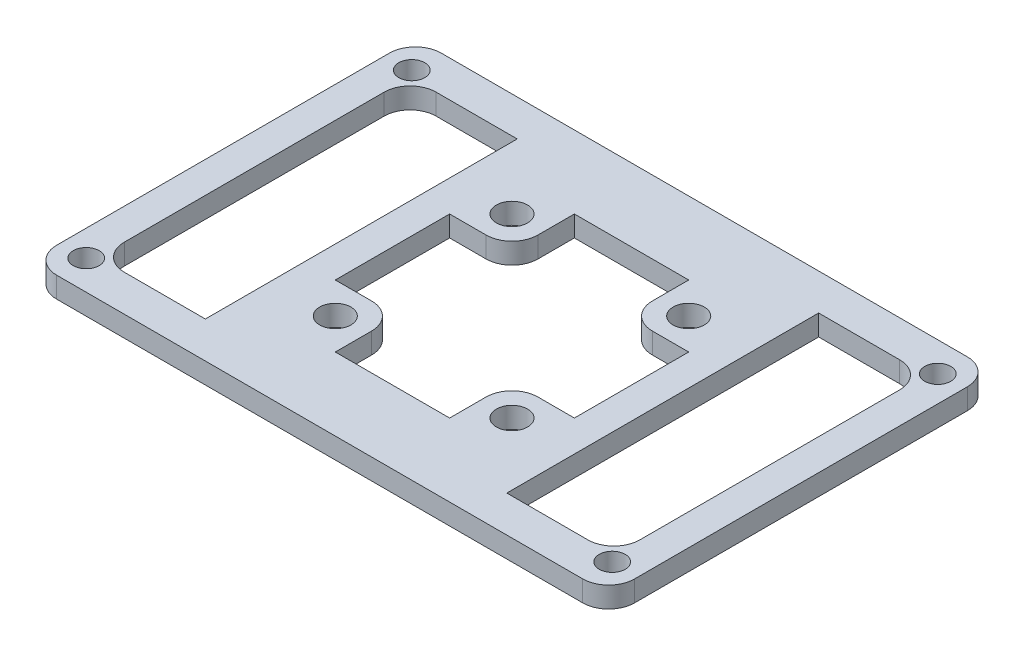
SolidWorks part; units mm, degrees
ref_plane "Front Plane" through (0, 0, 0) normal (0, 0, 1) x (1, 0, 0)
ref_plane "Top Plane" through (0, 0, 0) normal (0, 1, 0) x (1, 0, 0)
ref_plane "Right Plane" through (0, 0, 0) normal (1, 0, 0) x (0, 0, -1)
sketch "Sketch1" plane through (0, 0, 0) normal (0, 1, 0) x (1, 0, 0)
  line L1 (-27.8, 18.5) -> (27.8, 18.5)
  line L2 (-27.8, 18.5) -> (-27.8, -18.5)
  line L3 (-27.8, -18.5) -> (27.8, -18.5)
  line L4 (27.8, 18.5) -> (27.8, -18.5)
  line L5 (-27.8, 18.5) -> (27.8, -18.5) construction
  line L6 (-27.8, -18.5) -> (27.8, 18.5) construction
  point P0 (0, 0)
  dimension "D1" = 37
  dimension "D2" = 55.6
extrude "Boss-Extrude1" add sketch "Sketch1" along normal blind 2
sketch "Sketch3" plane through (0, 2, 0) normal (0, 1, 0) x (1, 0, 0)
  line L0 (0, 8.5) -> (0, -8.5) construction
  line L1 (-8.5, 8.5) -> (8.5, 8.5)
  line L2 (-8.5, 8.5) -> (-8.5, -8.5)
  line L3 (-8.5, -8.5) -> (8.5, -8.5)
  line L4 (8.5, 8.5) -> (8.5, -8.5)
  line L5 (-8.5, 8.5) -> (8.5, -8.5) construction
  line L6 (-8.5, -8.5) -> (8.5, 8.5) construction
  line L7 (-8.5, 0) -> (8.5, 0) construction
  circle A0 centre (-8.5, 8.5) radius 1.5
  circle A1 centre (-8.5, 8.5) radius 2.5
  circle A2 centre (-8.5, -8.5) radius 2.5
  circle A3 centre (-8.5, -8.5) radius 1.5
  circle A4 centre (8.5, -8.5) radius 1.5
  circle A5 centre (8.5, -8.5) radius 2.5
  circle A6 centre (8.5, 8.5) radius 2.5
  circle A7 centre (8.5, 8.5) radius 1.5
  point P0 (0, 0)
  dimension "D3" = 3
  dimension "D4" = 5
  dimension "D1" = 17
  dimension "D2" = 17
sketch "Sketch5" plane through (0, 2, 0) normal (0, 1, 0) x (1, 0, 0)
  line L0 (0, 11.5) -> (0, -11.5) construction
  line L5 (-11.5, 11.5) -> (11.5, 11.5)
  line L6 (-11.5, 11.5) -> (-11.5, -11.5)
  line L15 (-11.5, -11.5) -> (11.5, -11.5)
  line L16 (11.5, 11.5) -> (11.5, -11.5)
  line L21 (-11.5, 11.5) -> (11.5, -11.5) construction
  line L22 (-11.5, -11.5) -> (11.5, 11.5) construction
  line L23 (-11.5, 11.5) -> (-5.5, 11.5)
  line L24 (-11.5, 11.5) -> (-11.5, 5.5)
  line L25 (-11.5, 5.5) -> (-8, 5.5)
  line L26 (-5.5, 11.5) -> (-5.5, 8)
  line L27 (-11.5, 0) -> (11.5, 0) construction
  line L28 (11.5, 5.5) -> (8, 5.5)
  line L29 (5.5, 11.5) -> (5.5, 8)
  line L30 (11.5, 11.5) -> (5.5, 11.5)
  line L31 (11.5, 11.5) -> (11.5, 5.5)
  line L32 (11.5, -11.5) -> (5.5, -11.5)
  line L33 (5.5, -11.5) -> (5.5, -8)
  line L34 (11.5, -5.5) -> (8, -5.5)
  line L35 (11.5, -11.5) -> (11.5, -5.5)
  line L36 (-11.5, -5.5) -> (-8, -5.5)
  line L37 (-5.5, -11.5) -> (-5.5, -8)
  line L38 (-11.5, -11.5) -> (-5.5, -11.5)
  line L39 (-11.5, -11.5) -> (-11.5, -5.5)
  arc A0 (5.5, -8) -> (8, -5.5) centre (8, -8) cw
  arc A1 (-8, -5.5) -> (-5.5, -8) centre (-8, -8) cw
  arc A2 (8, 5.5) -> (5.5, 8) centre (8, 8) cw
  arc A3 (-8, 5.5) -> (-5.5, 8) centre (-8, 8) ccw
  point P0 (0, 0)
  point P25 (5.5, -5.5)
  point P28 (-5.5, -5.5)
  point P31 (5.5, 5.5)
  point P34 (-5.5, 5.5)
  dimension "D4" = 2.5
  dimension "D1" = 23
  dimension "D2" = 23
  dimension "D3" = 6
extrude "Cut-Extrude2" cut sketch "Sketch5" against normal up to next
fillet "Fillet2" radius 2.5 4 edges at (27.8, 1, -18.5) (-27.8, 1, -18.5) (27.8, 1, 18.5) (-27.8, 1, 18.5)
sketch "Sketch6" plane through (0, 2, 0) normal (0, 1, 0) x (1, 0, 0)
  line L0 (-27.8, 0) -> (-11.5, 0) construction
  line L1 (-27.8, 16) -> (-27.8, -16) construction
  line L2 (-11.5, 5.5) -> (-11.5, -5.5) construction
  line L3 (25.3, 18.5) -> (-25.3, 18.5) construction
  line L4 (-22.3, 15) -> (-14.5, 15)
  line L5 (-24.8, 12.5) -> (-24.8, -12.5)
  line L6 (-22.3, -15) -> (-14.5, -15)
  line L7 (-14.5, 15) -> (-14.5, -15)
  line L8 (-24.8, 15) -> (-14.5, -15) construction
  line L9 (-24.8, -15) -> (-14.5, 15) construction
  line L10 (0, 18.5) -> (0, -18.5) construction
  line L11 (-25.3, -18.5) -> (25.3, -18.5) construction
  line L12 (22.3, -15) -> (14.5, -15)
  line L13 (14.5, 15) -> (14.5, -15)
  line L14 (22.3, 15) -> (14.5, 15)
  line L15 (24.8, 12.5) -> (24.8, -12.5)
  arc A0 (-24.8, -12.5) -> (-22.3, -15) centre (-22.3, -12.5) ccw
  arc A1 (-22.3, 15) -> (-24.8, 12.5) centre (-22.3, 12.5) ccw
  arc A2 (24.8, -12.5) -> (22.3, -15) centre (22.3, -12.5) cw
  arc A3 (22.3, 15) -> (24.8, 12.5) centre (22.3, 12.5) cw
  point P6 (-19.65, 0)
  point P11 (-18.4, 15)
  point P14 (-24.8, 0)
  dimension "D3" = 2.5
  dimension "D1" = 3.5
  dimension "D2" = 3
extrude "Cut-Extrude3" cut sketch "Sketch6" against normal up to next
sketch "Sketch7" plane through (0, 2, 0) normal (0, 1, 0) x (1, 0, 0)
  line L0 (25.3, 18.5) -> (-25.3, 18.5) construction
  line L1 (-27.8, 16) -> (-27.8, -16) construction
  line L2 (0, 18.5) -> (0, -18.5) construction
  line L3 (-25.3, -18.5) -> (25.3, -18.5) construction
  line L4 (-27.8, 0) -> (27.8, 0) construction
  line L5 (27.8, -16) -> (27.8, 16) construction
  circle A0 centre (-25.3, 15.66) radius 1.25
  circle A1 centre (25.3, 15.66) radius 1.25
  circle A2 centre (25.3, -15.66) radius 1.25
  circle A3 centre (-25.3, -15.66) radius 1.25
  dimension "D3" = 2.5
  dimension "D1" = 2.84
  dimension "D2" = 2.5
extrude "Cut-Extrude4" cut sketch "Sketch7" against normal up to next
extrude "Cut-Extrude5" cut sketch "Sketch3" against normal blind 10 contours L1 A0 L2 | A7 L1 L4 | A7 L4 L1 | L2 A0 L1 | A3 L2 L3 | A3 L3 L2 | L4 A4 L3 | L3 A4 L4
